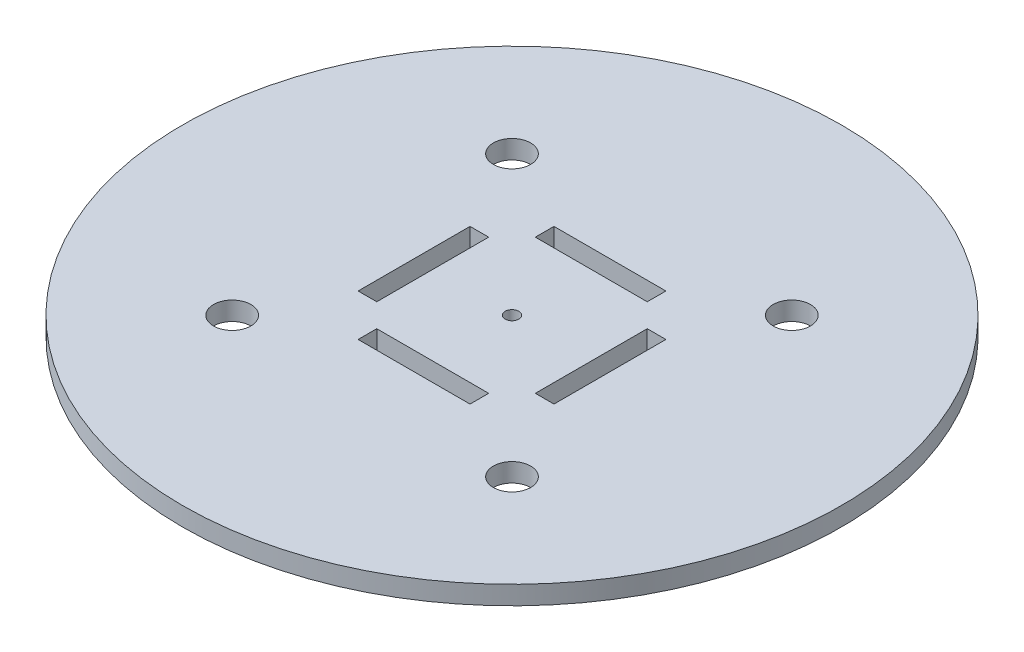
SolidWorks part; units mm, degrees
ref_plane "Front Plane" through (0, 0, 0) normal (0, 0, 1) x (1, 0, 0)
ref_plane "Top Plane" through (0, 0, 0) normal (0, 1, 0) x (1, 0, 0)
ref_plane "Right Plane" through (0, 0, 0) normal (1, 0, 0) x (0, 0, -1)
sketch "Sketch1" plane through (0, 0, 0) normal (0, 1, 0) x (1, 0, 0)
  circle A0 centre (0, 0) radius 53
  dimension "D1" = 106
extrude "Boss-Extrude1" add sketch "Sketch1" along normal blind 3
sketch "Sketch2" plane through (0, 3, 0) normal (0, 1, 0) x (1, 0, 0)
  line L1 (-9, 15.75) -> (9, 15.75)
  line L2 (-9, 15.75) -> (-9, 12.75)
  line L3 (-9, 12.75) -> (9, 12.75)
  line L4 (9, 15.75) -> (9, 12.75)
  line L5 (-15.75, 9) -> (-12.75, 9)
  line L6 (-15.75, 9) -> (-15.75, -9)
  line L7 (-15.75, -9) -> (-12.75, -9)
  line L8 (-12.75, 9) -> (-12.75, -9)
  line L9 (-9, -12.75) -> (9, -12.75)
  line L10 (-9, -12.75) -> (-9, -15.75)
  line L11 (-9, -15.75) -> (9, -15.75)
  line L12 (9, -12.75) -> (9, -15.75)
  line L13 (12.75, 9) -> (15.75, 9)
  line L14 (12.75, 9) -> (12.75, -9)
  line L15 (12.75, -9) -> (15.75, -9)
  line L16 (15.75, 9) -> (15.75, -9)
  circle A0 centre (0, 0) radius 1.1
  dimension "D13" = 2.2
  dimension "D1" = 18
  dimension "D2" = 3
  dimension "D3" = 18
  dimension "D4" = 3
  dimension "D5" = 18
  dimension "D6" = 3
  dimension "D7" = 18
  dimension "D8" = 3
  dimension "D9" = 12.75
  dimension "D10" = 12.75
  dimension "D11" = 12.75
  dimension "D12" = 12.75
  dimension "D14" = 9
  dimension "D15" = 9
extrude "Cut-Extrude1" cut sketch "Sketch2" against normal blind 3
sketch "Sketch3" plane through (0, 3, 0) normal (0, 1, 0) x (1, 0, 0)
  text T0 "Neck" font "Century Gothic" height in points 22
  dimension "D1" = 10
  dimension "D2" = 3
sketch "Sketch4" plane through (0, 3, 0) normal (0, 1, 0) x (1, 0, 0)
  circle A0 centre (-22.5, 22.5) radius 3
  point P2 (0, 0)
  point P5 (-21.4103, 2.6208)
  dimension "D1" = 6
  dimension "D2" = 22.5
  dimension "D3" = 22.5
extrude "Cut-Extrude2" cut sketch "Sketch4" against normal blind 3
pattern_circular "CirPattern1" count 4 over 360 about axis through (0, 0, 0) along (0, 1, 0) of "Cut-Extrude2"
